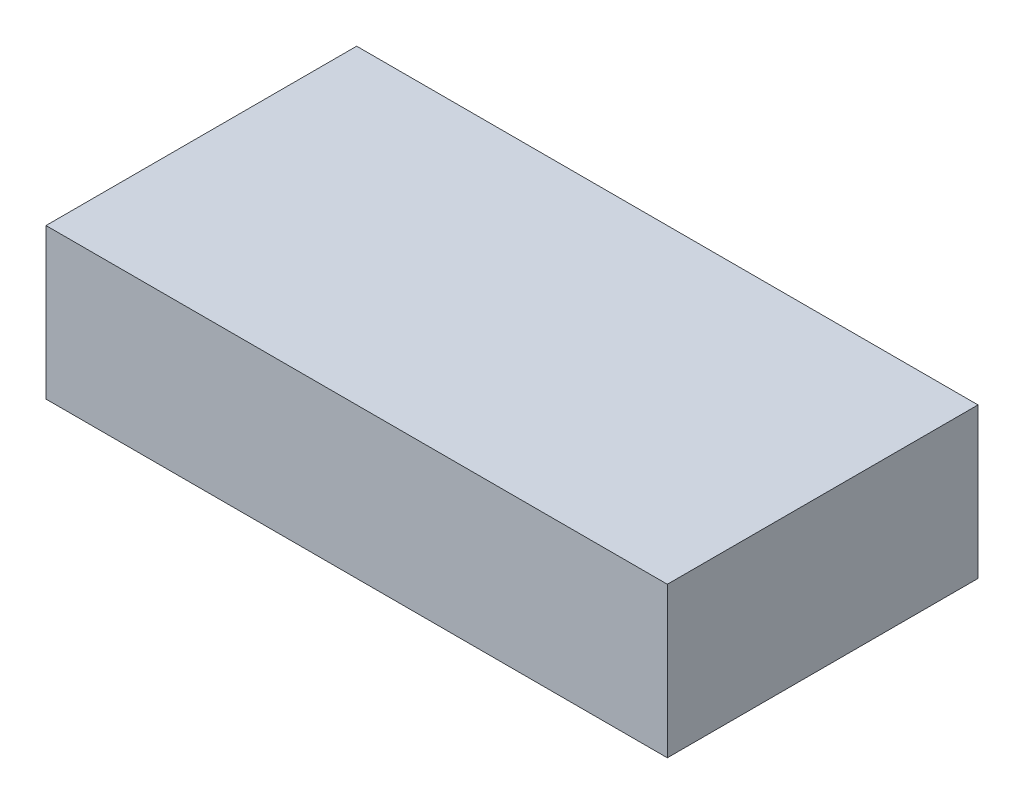
SolidWorks part; units mm, degrees
ref_plane "Front Plane" through (0, 0, 0) normal (0, 0, 1) x (1, 0, 0)
ref_plane "Top Plane" through (0, 0, 0) normal (0, 1, 0) x (1, 0, 0)
ref_plane "Right Plane" through (0, 0, 0) normal (1, 0, 0) x (0, 0, -1)
sketch "Sketch1" plane through (0, 0, 0) normal (0, 1, 0) x (1, 0, 0)
  line L0 (-31, -15.5) -> (31, -15.5)
  line L1 (-31, -15.5) -> (-31, 15.5)
  line L2 (31, -15.5) -> (31, 15.5)
  line L3 (-31, 15.5) -> (31, 15.5)
  line L4 (-31, -15.5) -> (31, 15.5) construction
  line L5 (31, -15.5) -> (-31, 15.5) construction
  point P1 (0, 0)
  dimension "D1" = 62
  dimension "D2" = 31
extrude "Boss-Extrude1" add sketch "Sketch1" along normal blind 15
